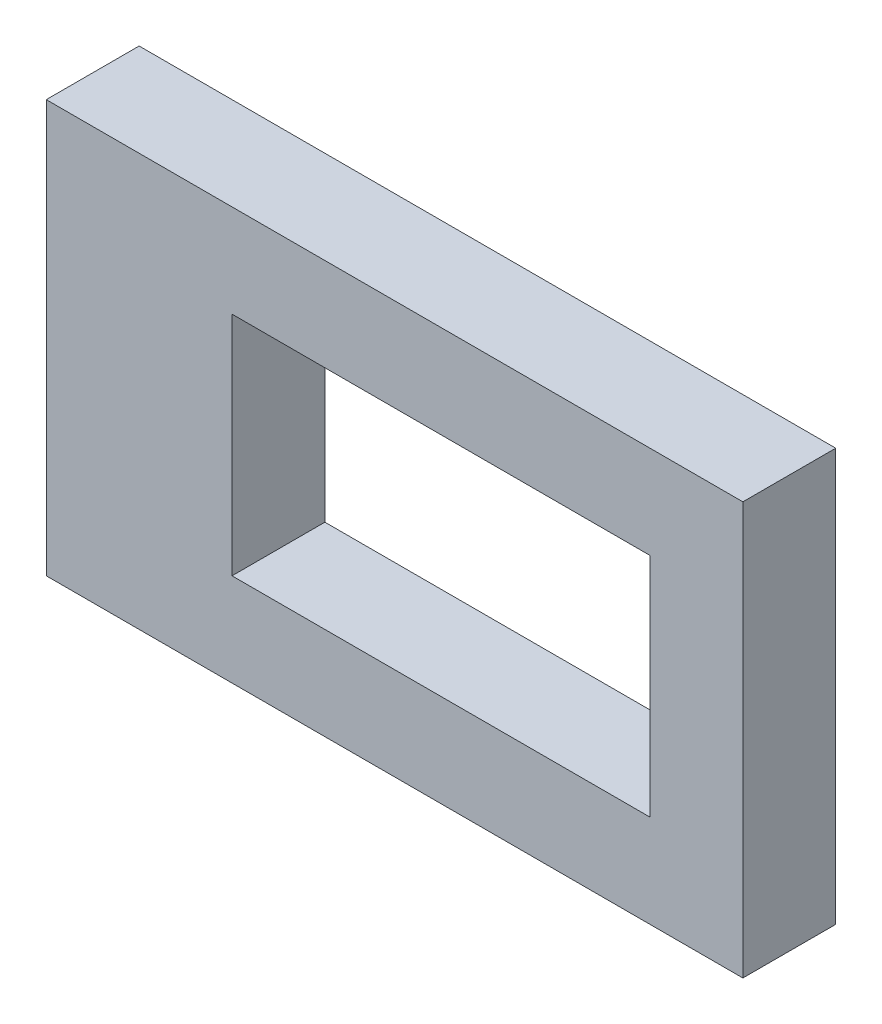
SolidWorks part; units mm, degrees
ref_plane "Front Plane" through (0, 0, 0) normal (0, 0, 1) x (1, 0, 0)
ref_plane "Top Plane" through (0, 0, 0) normal (0, 1, 0) x (1, 0, 0)
ref_plane "Right Plane" through (0, 0, 0) normal (1, 0, 0) x (0, 0, -1)
sketch "Sketch1" plane through (0, 0, 0) normal (0, 0, 1) x (1, 0, 0)
  line L1 (0, 0) -> (-22.5, 0)
  line L2 (0, 0) -> (0, 12.2)
  line L3 (0, 12.2) -> (-22.5, 12.2)
  line L4 (-22.5, 0) -> (-22.5, 12.2)
  line L5 (5, -5) -> (-32.5, -5)
  line L6 (5, -5) -> (5, 17.2)
  line L7 (5, 17.2) -> (-32.5, 17.2)
  line L8 (-32.5, -5) -> (-32.5, 17.2)
  dimension "D1" = 22.5
  dimension "D2" = 12.2
  dimension "D3" = 5
  dimension "D4" = 5
  dimension "D5" = 5
  dimension "D6" = 10
extrude "Boss-Extrude1" add sketch "Sketch1" along normal blind 5
